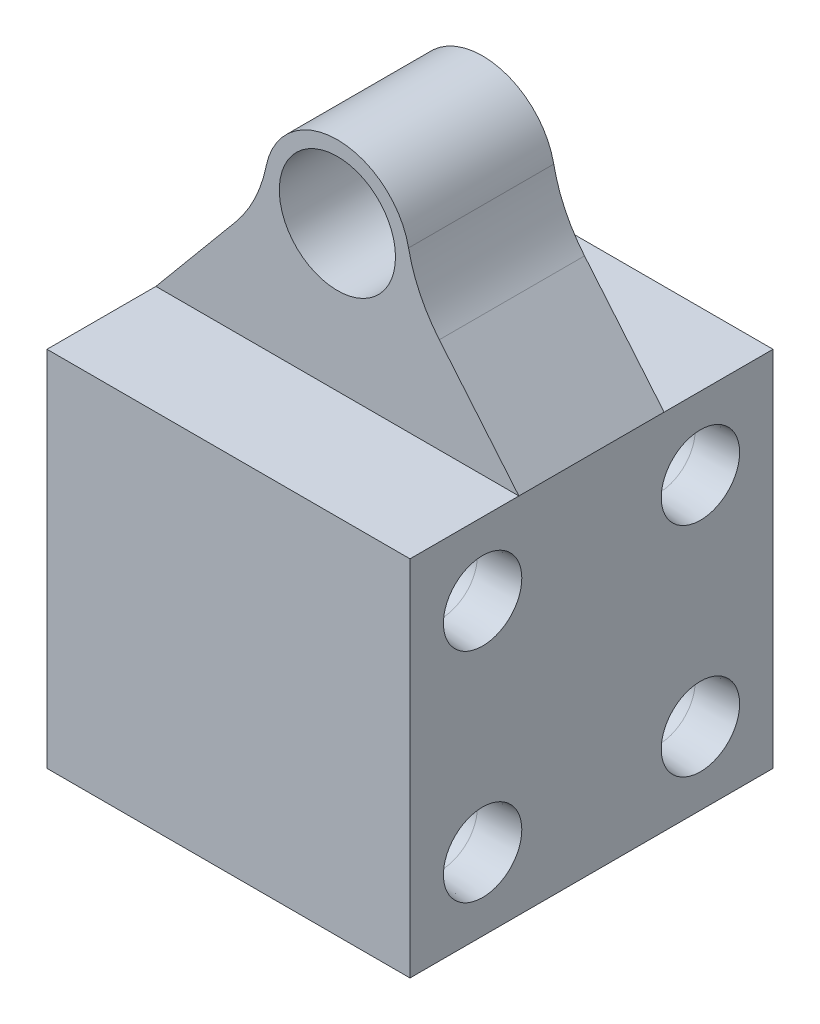
SolidWorks part; units mm, degrees
ref_plane "Front Plane" through (0, 0, 0) normal (0, 0, 1) x (1, 0, 0)
ref_plane "Top Plane" through (0, 0, 0) normal (0, 1, 0) x (1, 0, 0)
ref_plane "Right Plane" through (0, 0, 0) normal (1, 0, 0) x (0, 0, -1)
sketch "Sketch2" plane through (0, 0, 0) normal (0, 1, 0) x (1, 0, 0)
  line L1 (-12.5, 12.5) -> (12.5, 12.5)
  line L2 (-12.5, 12.5) -> (-12.5, -12.5)
  line L3 (-12.5, -12.5) -> (12.5, -12.5)
  line L4 (12.5, 12.5) -> (12.5, -12.5)
  line L5 (-12.5, 12.5) -> (12.5, -12.5) construction
  line L6 (-12.5, -12.5) -> (12.5, 12.5) construction
  point P0 (0, 0)
  dimension "D1" = 25
  dimension "D2" = 25
extrude "Boss-Extrude1" add sketch "Sketch2" along normal blind 25
hole_wizard "CSK for M3 Oval Head Machine Screw1" positions "Sketch3" profile "Sketch4" countersink size "M3" standard "ANSI Metric"
sketch "Sketch3" plane through (-12.5, 0, 0) normal (-1, 0, 0) x (0, 0, 1)
  line L0 (-12.5, 25) -> (12.5, 25) construction
  line L1 (-12.5, 25) -> (-12.5, 0) construction
  point P0 (-7.5, 20)
  dimension "D1" = 5
  dimension "D2" = 5
sketch "Sketch4" plane through (-12.5, 20, -7.5) normal (0, 1, 0) x (0, 0, 1)
  line L0 (0, 0) -> (0, 11.5022)
  line L1 (0, 11.5022) -> (2.5, 10)
  line L2 (2.5, 10) -> (2.5, 2.8601)
  line L3 (2.5, 2.8601) -> (2.7, 0)
  line L5 (2.7, 0) -> (0, 0)
  line L6 (-2.5, 2.8601) -> (-2.7, 0) construction
  line L10 (0, 11.5022) -> (-2.5, 10) construction
  line L11 (0, -6.35) -> (0, 107.95) construction
  dimension "Hole Dia." = 5
  dimension "Hole Depth" = 10
  dimension "Near C'Sink Dia." = 5.4
  dimension "Near C'Sink Angle" = 8
  dimension "Drill Angle" = 118
pattern_linear "LPattern1" count 2 spacing 15 along (0, -1, 0) count 2 spacing 15 along (0, 0, 1) of "CSK for M3 Oval Head Machine Screw1"
mirror "Mirror1" about plane through (0, 0, 0) normal (1, 0, 0) of "LPattern1", "CSK for M3 Oval Head Machine Screw1"
sketch "Sketch6" plane through (0, 0, 0) normal (0, 0, 1) x (1, 0, 0)
  line L0 (0, 40) -> (-12.5, 25)
  line L1 (0, 40) -> (12.5, 25)
  line L2 (-12.5, 25) -> (12.5, 25)
  line L3 (12.5, 25) -> (-12.5, 25) construction
  circle A0 centre (0, 35) radius 4
  circle A1 centre (0, 35) radius 5
  dimension "D1" = 8
  dimension "D2" = 10
  dimension "D3" = 10
extrude "Boss-Extrude3" add sketch "Sketch6" along normal blind 5 and the other way blind 5 contours A1 L0 L2 L1 | A0
fillet "Fillet4" radius 10 2 edges at (-4.918, 34.0984, 0) (4.918, 34.0984, 0)
